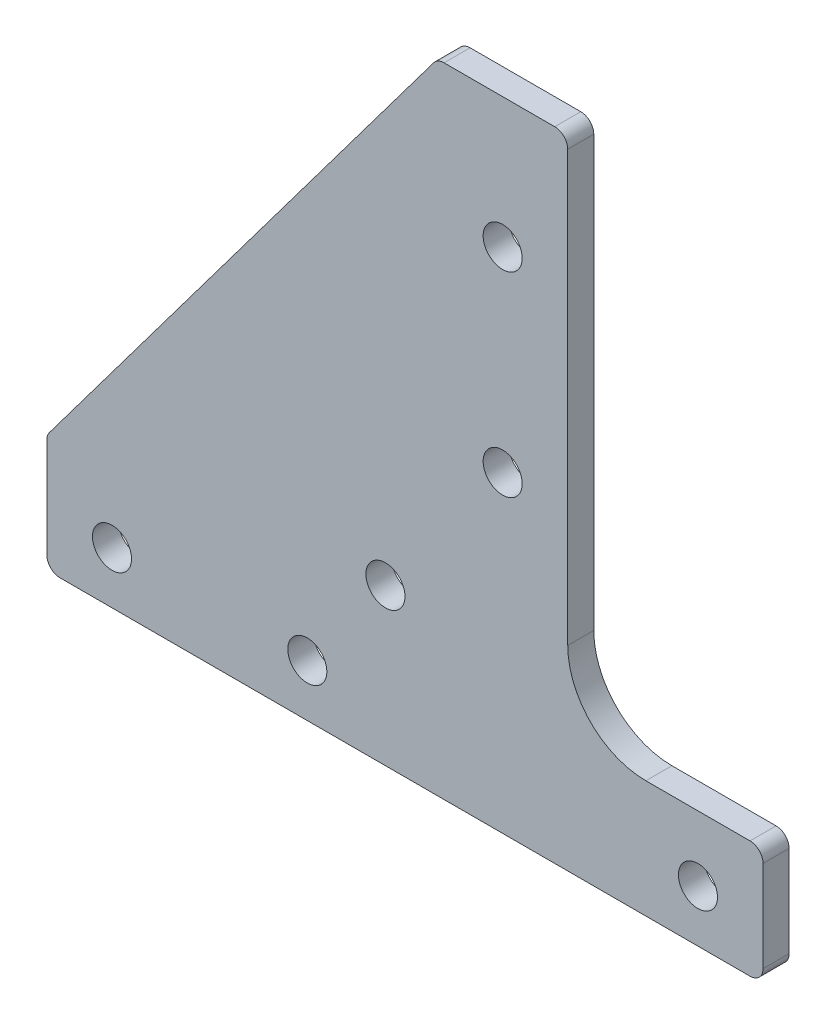
SolidWorks part; units mm, degrees
material "环氧板3240"
ref_plane "前视基准面" through (0, 0, 0) normal (0, 0, 1) x (1, 0, 0)
ref_plane "上视基准面" through (0, 0, 0) normal (0, 1, 0) x (1, 0, 0)
ref_plane "右视基准面" through (0, 0, 0) normal (1, 0, 0) x (0, 0, -1)
other "Configuration Table"
sketch "草图1" plane through (0, 0, 0) normal (0, 0, 1) x (1, 0, 0)
  line L1 (-35, 5) -> (-5, 45)
  line L3 (-5, 45) -> (5, 45)
  line L4 (5, 45) -> (5, 15) construction
  line L6 (-35, -5) -> (-35, 5)
  line L7 (-35, 0) -> (0, 0) construction
  line L8 (0, 45) -> (0, 0) construction
  line L10 (20, -5) -> (-35, -5) construction
  line L11 (-35, -4) -> (20, -4)
  line L12 (5, 15) -> (-14, -4) construction
  line L13 (5, 45) -> (20, 5)
  line L14 (20, 5) -> (20, -5)
  line L16 (0, 0) -> (20, 0) construction
  line L18 (-12.1754, 8) -> (-10.5877, 5.25) construction
  line L25 (-10.5877, 5.25) -> (-7.4123, 5.25) construction
  line L26 (-7.4123, 5.25) -> (-5.8246, 8) construction
  line L27 (-5.8246, 8) -> (-7.4123, 10.75) construction
  line L28 (-7.4123, 10.75) -> (-10.5877, 10.75) construction
  line L29 (-10.5877, 10.75) -> (-12.1754, 8) construction
  circle A0 centre (-30, 0) radius 1.5
  circle A1 centre (0, 35) radius 1.5
  circle A2 centre (-15, 0) radius 1.5
  circle A3 centre (0, 20) radius 1.5
  circle A5 centre (-9, 8) radius 1.5
  circle A6 centre (0, 0) radius 1.5 construction
  circle A8 centre (15, 0) radius 1.5
  circle A9 centre (-9, 8) radius 4 construction
  circle A10 centre (-9, 8) radius 2.75 construction
  dimension "D7" = 3
  dimension "D8" = 15
  dimension "D9" = 15
  dimension "D10" = 20
  dimension "D11" = 15
  dimension "D12" = 10
  dimension "D13" = 8
  dimension "D14" = 9
  dimension "D15" = 5
  dimension "D18" = 8
  dimension "D1" = 10
  dimension "D2" = 20
  dimension "D3" = 50
  dimension "D4" = 35
  dimension "D5" = 45
  dimension "D6" = 1
  dimension "D17" = 15
  dimension "D19" = 5.5
extrude "凸台-拉伸1" add sketch "草图1" along normal blind 2
sketch "草图2" plane through (0, 0, 2) normal (0, 0, 1) x (1, 0, 0)
  line L0 (5, 45) -> (5, 11)
  line L1 (11, 5) -> (20, 5)
  line L2 (5, 45) -> (20, 5)
  line L3 (5, 45) -> (20, 5) construction
  arc A1 (11, 5) -> (5, 11) centre (11, 11) cw
  point P11 (5, 5)
  point P15 (5, 5)
  dimension "D1" = 6
extrude "切除-拉伸1" cut sketch "草图2" against normal blind 10
fillet "圆角1" radius 1 6 edges at (-5, 45, 1) (5, 45, 1) (20, 5, 1) (20, -4, 1) (-35, 5, 1) (-35, -4, 1)
